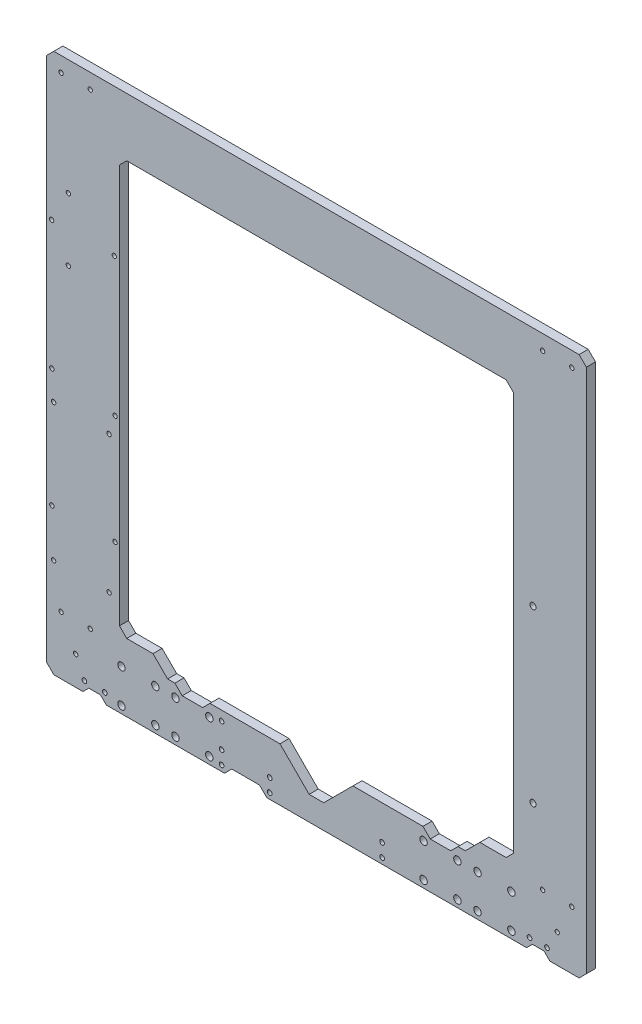
SolidWorks part; units mm, degrees
ref_plane "Front Plane" through (0, 0, 0) normal (0, 0, 1) x (1, 0, 0)
ref_plane "Top Plane" through (0, 0, 0) normal (0, 1, 0) x (1, 0, 0)
ref_plane "Right Plane" through (0, 0, 0) normal (1, 0, 0) x (0, 0, -1)
sketch "Sketch1" plane through (0, 0, 0) normal (0, 0, 1) x (1, 0, 0)
  line L0 (-92, -141.75) -> (-97, -136.75)
  line L1 (-97, -136.75) -> (-102, -136.75)
  line L2 (-102, -136.75) -> (-112, -126.75)
  line L3 (-112, -126.75) -> (-130, -126.75)
  line L4 (-130, -126.75) -> (-135, -121.75)
  line L5 (-135, -121.75) -> (-135, 151.75)
  line L6 (-135, 151.75) -> (-130, 156.75)
  line L7 (-130, 156.75) -> (130, 156.75)
  line L8 (130, 156.75) -> (135, 151.75)
  line L9 (135, 151.75) -> (135, -121.75)
  line L10 (135, -121.75) -> (130, -126.75)
  line L11 (130, -126.75) -> (112, -126.75)
  line L12 (112, -126.75) -> (102, -136.75)
  line L13 (102, -136.75) -> (97, -136.75)
  line L14 (97, -136.75) -> (92, -141.75)
  line L15 (92, -141.75) -> (78, -141.75)
  line L16 (78, -141.75) -> (73, -136.75)
  line L17 (73, -136.75) -> (25, -136.75)
  line L18 (25, -136.75) -> (5, -156.75)
  line L19 (5, -156.75) -> (-5, -156.75)
  line L20 (-5, -156.75) -> (-25, -136.75)
  line L21 (-25, -136.75) -> (-73, -136.75)
  line L22 (-73, -136.75) -> (-78, -141.75)
  line L23 (-78, -141.75) -> (-92, -141.75)
  line L24 (180, 196.75) -> (-180, 196.75)
  line L25 (-180, 196.75) -> (-185, 191.75)
  line L26 (-185, 191.75) -> (-185, -168.25)
  line L27 (-185, -168.25) -> (-180, -173.25)
  line L28 (-180, -173.25) -> (-160, -173.25)
  line L29 (-160, -173.25) -> (-156, -169.25)
  line L30 (-156, -169.25) -> (-148, -169.25)
  line L31 (-148, -169.25) -> (-144, -173.25)
  line L32 (-144, -173.25) -> (-63, -173.25)
  line L33 (-63, -173.25) -> (-58, -168.25)
  line L34 (-58, -168.25) -> (-39, -168.25)
  line L35 (-39, -168.25) -> (-34, -173.25)
  line L36 (-34, -173.25) -> (144, -173.25)
  line L37 (144, -173.25) -> (148, -169.25)
  line L38 (148, -169.25) -> (156, -169.25)
  line L39 (156, -169.25) -> (160, -173.25)
  line L40 (160, -173.25) -> (180, -173.25)
  line L41 (180, -173.25) -> (185, -168.25)
  line L42 (185, -168.25) -> (185, 191.75)
  line L43 (185, 191.75) -> (180, 196.75)
  line L44 (0, 156.75) -> (0, -156.75) construction
  circle A0 centre (165, -153.45) radius 1.5
  circle A1 centre (-155, 186.55) radius 1.5
  circle A2 centre (-175, -133.45) radius 1.5
  circle A3 centre (-65, -143.25) radius 1.6
  circle A4 centre (-175, 186.55) radius 1.5
  circle A5 centre (-180.1, -11.45) radius 1.5
  circle A6 centre (-181.5, 96.05) radius 1.5
  circle A7 centre (-181.3, 7.85) radius 1.5
  circle A8 centre (-138, 1.45) radius 1.5
  circle A9 centre (-138.5, 96.05) radius 1.5
  circle A10 centre (-165, -153.45) radius 1.5
  circle A11 centre (-181.3, -73.45) radius 1.5
  circle A12 centre (175, 186.55) radius 1.5
  circle A13 centre (-170, 74.55) radius 1.5
  circle A14 centre (-138, -73.45) radius 1.5
  circle A15 centre (155, -133.45) radius 1.5
  circle A16 centre (175, -133.45) radius 1.5
  circle A17 centre (-180.1, -105.45) radius 1.5
  circle A18 centre (155, 186.55) radius 1.5
  circle A19 centre (-170, 117.55) radius 1.5
  circle A20 centre (-159, -166.25) radius 1.6
  circle A21 centre (133.6, -168.35) radius 2.55
  circle A22 centre (-145, -166.25) radius 1.6
  circle A23 centre (96.6, -145.15) radius 2.55
  circle A24 centre (73.4, -168.35) radius 2.55
  circle A25 centre (-73.4, -168.35) radius 2.55
  circle A26 centre (96.6, -168.35) radius 2.55
  circle A27 centre (-73.4, -145.15) radius 2.55
  circle A28 centre (-110.4, -168.35) radius 2.55
  circle A29 centre (-133.6, -168.35) radius 2.55
  circle A30 centre (-110.4, -145.15) radius 2.55
  circle A31 centre (73.4, -145.15) radius 2.55
  circle A32 centre (146, -166.25) radius 1.6
  circle A33 centre (-133.6, -145.15) radius 2.55
  circle A34 centre (110.4, -145.15) radius 2.55
  circle A35 centre (-96.6, -145.15) radius 2.55
  circle A36 centre (110.4, -168.35) radius 2.55
  circle A37 centre (133.6, -145.15) radius 2.55
  circle A38 centre (-96.6, -168.35) radius 2.55
  circle A39 centre (158, -166.25) radius 1.6
  circle A40 centre (-65, -160.25) radius 1.6
  circle A41 centre (-65, -169.25) radius 1.6
  circle A42 centre (45, -160.25) radius 1.6
  circle A43 centre (148.4, 31.75) radius 2.1
  circle A44 centre (45, -169.25) radius 1.6
  circle A45 centre (148.4, -85.25) radius 2.1
  circle A46 centre (-32, -160.25) radius 1.6
  circle A47 centre (-32, -169.25) radius 1.6
  circle A48 centre (-142.1, -11.45) radius 1.5
  circle A49 centre (-155, -133.45) radius 1.5
  circle A50 centre (-142.1, -105.45) radius 1.5
extrude "Boss-Extrude1" add sketch "Sketch1" against normal blind 6.25
